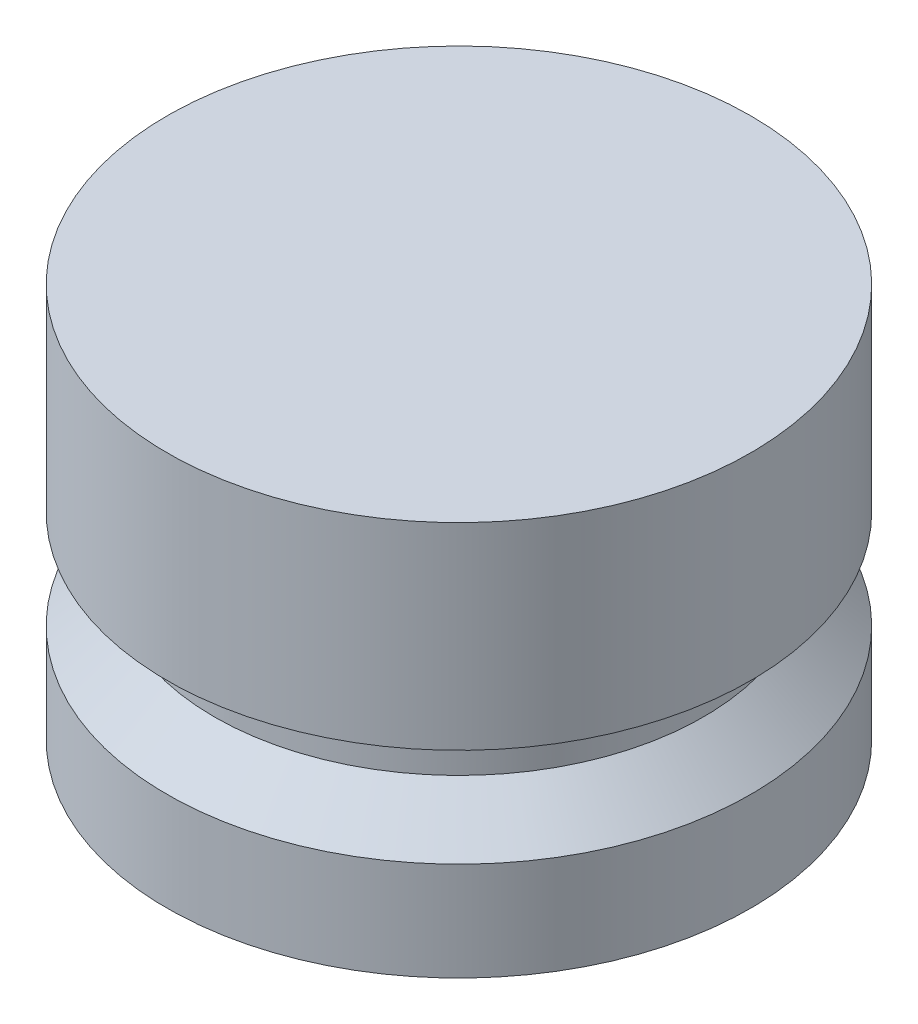
SolidWorks part; units mm, degrees
ref_plane "Front Plane" through (0, 0, 0) normal (0, 0, 1) x (1, 0, 0)
ref_plane "Top Plane" through (0, 0, 0) normal (0, 1, 0) x (1, 0, 0)
ref_plane "Right Plane" through (0, 0, 0) normal (1, 0, 0) x (0, 0, -1)
sketch "Sketch1" plane through (0, 0, 0) normal (0, 0, 1) x (1, 0, 0)
  line L0 (0, 0) -> (0, 12.7) construction
  line L1 (0, 0) -> (-9.398, 0)
  line L2 (-9.398, 0) -> (-9.398, 3.175)
  line L4 (-7.874, 4.572) -> (-7.874, 6.35)
  line L5 (-7.874, 6.35) -> (-9.398, 6.35)
  line L6 (-9.398, 6.35) -> (-9.398, 12.7)
  line L7 (-9.398, 12.7) -> (0, 12.7)
  line L8 (-9.525, 16.6801) -> (-9.525, -9.6051) construction
  line L9 (0, 0) -> (0, 12.7)
  line L10 (-7.874, 4.572) -> (-9.398, 3.175)
  dimension "D1" = 12.7
  dimension "D2" = 9.398
  dimension "D3" = 1.778
  dimension "D4" = 3.175
  dimension "D5" = 9.525
  dimension "D6" = 7.874
  dimension "D7" = 6.35
revolve "Revolve1" add sketch "Sketch1" angle 360 about L9
